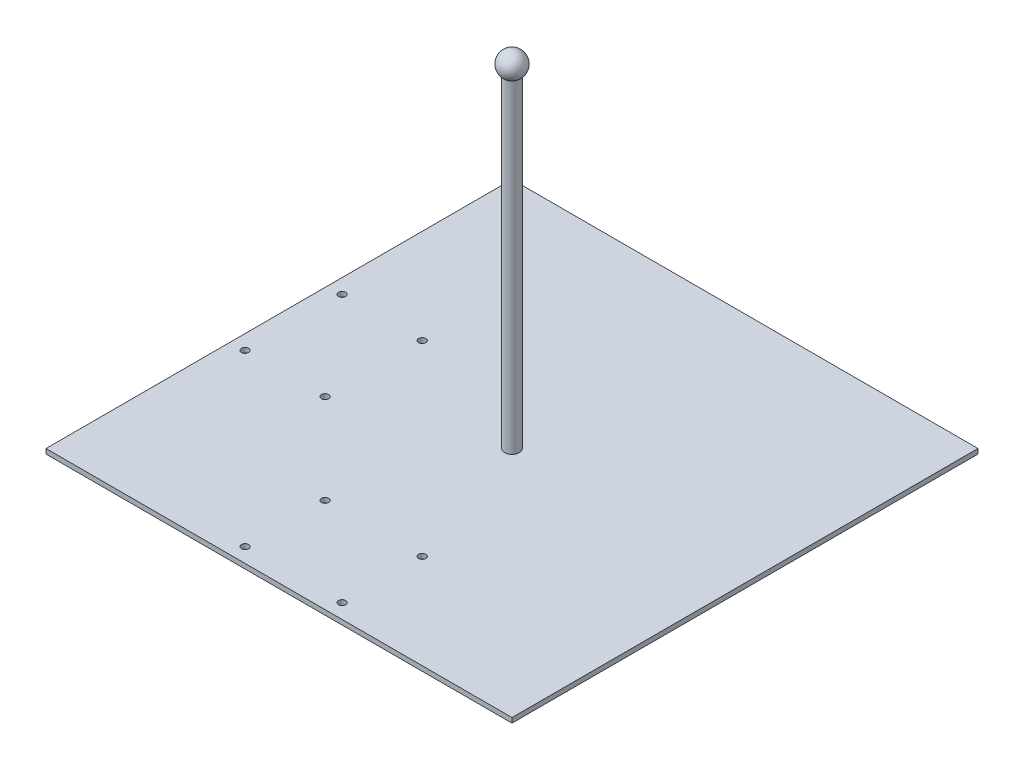
SolidWorks part; units mm, degrees
material "6061-T6 (SS)"
ref_plane "Front Plane" through (0, 0, 0) normal (0, 0, 1) x (1, 0, 0)
ref_plane "Top Plane" through (0, 0, 0) normal (0, 1, 0) x (1, 0, 0)
ref_plane "Right Plane" through (0, 0, 0) normal (1, 0, 0) x (0, 0, -1)
sketch "Sketch1" plane through (0, 0, 0) normal (0, 1, 0) x (1, 0, 0)
  line L1 (-304.8, -304.8) -> (304.8, -304.8)
  line L2 (-304.8, -304.8) -> (-304.8, 304.8)
  line L3 (-304.8, 304.8) -> (304.8, 304.8)
  line L4 (304.8, -304.8) -> (304.8, 304.8)
  dimension "D1" = 609.6
  dimension "D2" = 609.6
  dimension "D3" = 304.8
  dimension "D4" = 304.8
extrude "Boss-Extrude1" add sketch "Sketch1" along normal blind 6.35 contours L2 L3 L4 L1
hole_wizard "3/8 (0.375) Diameter Hole1" positions "Sketch2" profile "Sketch3" hole size "3/8" standard "ANSI Inch"
sketch "Sketch2" plane through (0, 6.35, 0) normal (0, 1, 0) x (1, 0, 0)
  line L1 (-304.8, -304.8) -> (-304.8, 304.8) construction
  line L3 (-304.8, -304.8) -> (304.8, -304.8) construction
  point P0 (-63.5, -285.75)
  point P2 (63.5, -285.75)
  point P4 (-285.75, 63.5)
  point P6 (-285.75, -63.5)
  point P17 (-304.8, 0)
  point P33 (-63.5, -180.975)
  point P35 (63.5, -180.975)
  point P37 (-180.975, -63.5)
  point P39 (-180.975, 63.5)
  dimension "D1" = 63.5
  dimension "D2" = 127
  dimension "D3" = 19.05
  dimension "D4" = 19.05
  dimension "D5" = 127
  dimension "D6" = 63.5
  dimension "D7" = 104.775
  dimension "D8" = 104.775
sketch "Sketch3" plane through (-63.5, 6.35, 285.75) normal (1, 0, 0) x (0, 0, 1)
  line L0 (0, 0) -> (0, 14.5456)
  line L1 (0, 14.5456) -> (4.7625, 11.684)
  line L2 (4.7625, 11.684) -> (4.7625, 0)
  line L5 (4.7625, 0) -> (0, 0)
  line L10 (0, 14.5456) -> (-4.7625, 11.684) construction
  line L11 (0, -6.35) -> (0, 107.95) construction
  dimension "Hole Dia." = 9.525
  dimension "Hole Depth" = 11.684
  dimension "Drill Angle" = 118
sketch "Sketch4" plane through (0, 6.35, 0) normal (0, 1, 0) x (1, 0, 0)
  circle A0 centre (0, 0) radius 9.525
  dimension "D1" = 19.05
extrude "Boss-Extrude2" add sketch "Sketch4" along normal blind 422.91
ref_axis "Axis1" through (0, 599.8237, 0) along (0, -1, 0)
sketch "Sketch5" plane through (0, 0, 0) normal (0, 0, 1) x (1, 0, 0)
  line L0 (0, 457.835) -> (0, 426.085)
  arc A0 (0, 457.835) -> (0, 426.085) centre (0, 441.96) ccw
  dimension "D1" = 31.75
revolve "Revolve3" add sketch "Sketch5" angle 360 about axis through (0, 599.8237, 0) along (0, -1, 0)
